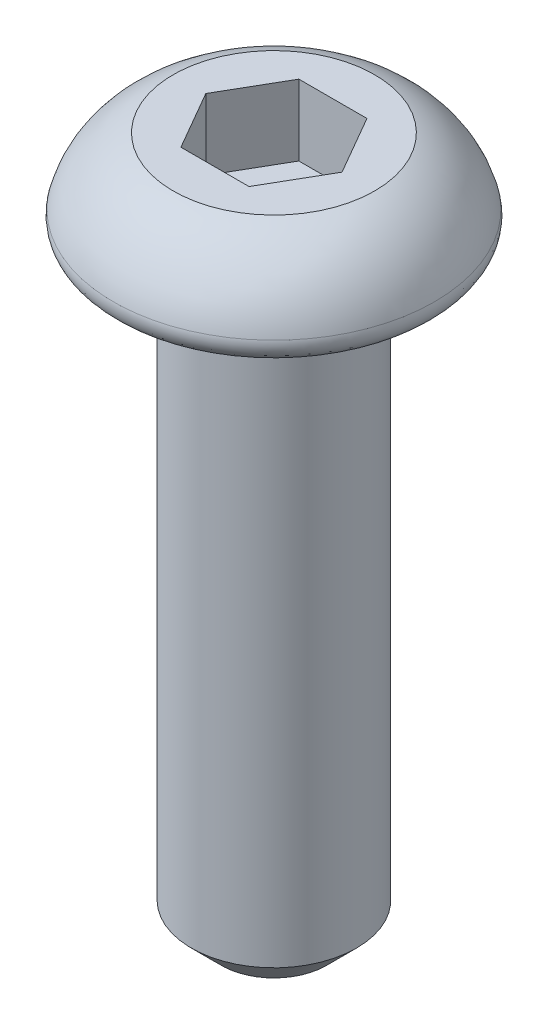
SolidWorks part; units mm, degrees
material "Alloy Steel"
ref_plane "Front Plane" through (0, 0, 0) normal (0, 0, 1) x (1, 0, 0)
ref_plane "Top Plane" through (0, 0, 0) normal (0, 1, 0) x (1, 0, 0)
ref_plane "Right Plane" through (0, 0, 0) normal (1, 0, 0) x (0, 0, -1)
sketch "Sketch1" plane through (0, 0, 0) normal (0, 0, 1) x (1, 0, 0)
  line L0 (1.5875, 1.4224) -> (0, 1.4224)
  line L1 (0, 1.4224) -> (0, 0)
  line L2 (0, 0) -> (2.2355, 0)
  line L3 (0, 1.4224) -> (0, -0.0172) construction
  arc A0 (2.5302, 0.381) -> (1.5875, 1.4224) centre (1.0628, 0) ccw
  spline S0 degree 3 poles (2.5302, 0.381) (2.5388, 0.348) (2.5418, 0.3131) (2.5389, 0.2791) (2.5361, 0.2452) (2.5274, 0.2112) (2.5134, 0.1801) (2.4995, 0.149) (2.48, 0.1199) (2.4566, 0.0951) (2.4332, 0.0704) (2.4052, 0.0494) (2.3749, 0.0338) (2.3446, 0.0182) (2.3112, 0.0076) (2.2774, 0.0029) (2.2635, 0.001) (2.2495, 0) (2.2355, 0) knots 0 0 0 0 0.000102 0.000102 0.000102 0.000204 0.000204 0.000204 0.000307 0.000307 0.000307 0.000409 0.000409 0.000409 0.000511 0.000511 0.000511 0.000553 0.000553 0.000553 0.000553
revolve "Revolve1" add sketch "Sketch1" angle 360 about L3
sketch "Sketch2" plane through (0, 0, 0) normal (0, -1, 0) x (1, 0, 0)
  circle A0 centre (0, 0) radius 1.3017
extrude "Boss-Extrude1" add sketch "Sketch2" along normal blind 9.525
sketch "Sketch3" plane through (0, 1.4224, 0) normal (0, 1, 0) x (-1, 0, 0)
  line L0 (0.5366, -0.9294) -> (1.0731, 0)
  line L1 (1.0731, 0) -> (0.5366, 0.9294)
  line L2 (0.5366, 0.9294) -> (-0.5366, 0.9294)
  line L3 (-0.5366, 0.9294) -> (-1.0731, 0)
  line L4 (-1.0731, 0) -> (-0.5366, -0.9294)
  line L5 (-0.5366, -0.9294) -> (0.5366, -0.9294)
extrude "Cut-Extrude1" cut sketch "Sketch3" against normal blind 1.1176
chamfer "Chamfer1" distance 0.4724 angle 45 1 edges at (0, -9.525, -1.3017)
fillet "Fillet1" radius 0.254 1 edges at (0, 0, -1.3017)
